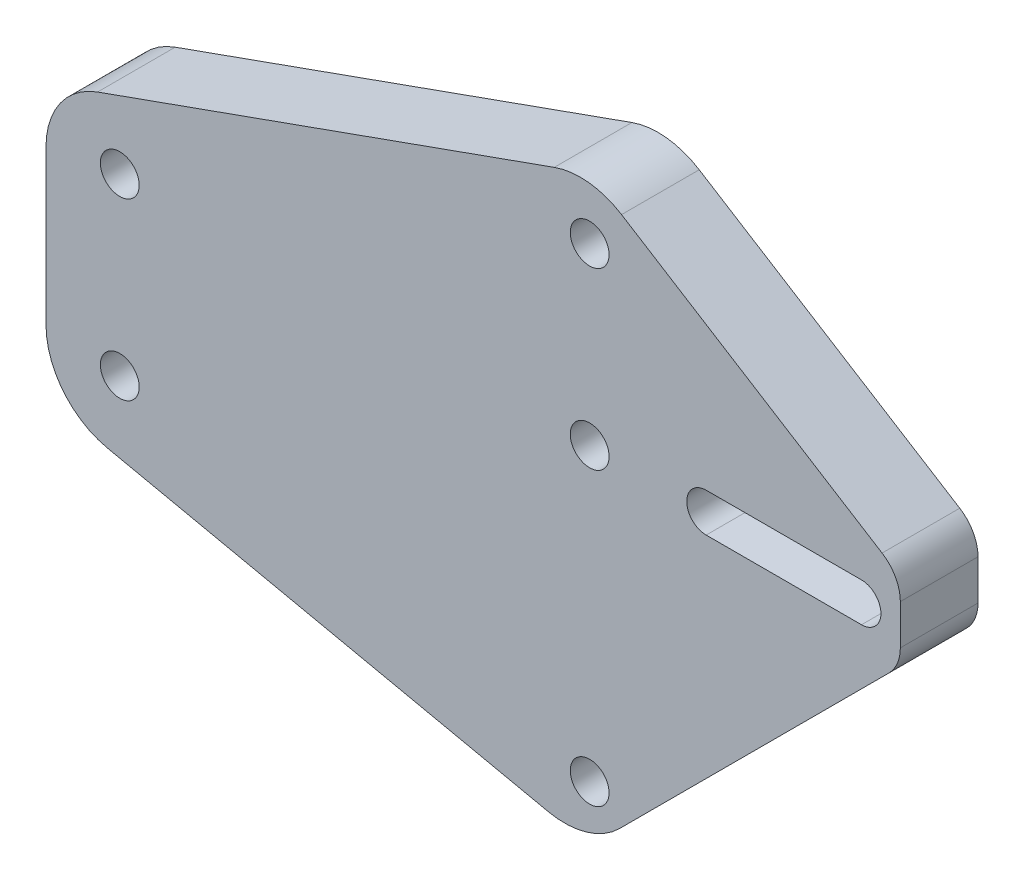
SolidWorks part; units mm, degrees
ref_plane "Front Plane" through (0, 0, 0) normal (0, 0, 1) x (1, 0, 0)
ref_plane "Top Plane" through (0, 0, 0) normal (0, 1, 0) x (1, 0, 0)
ref_plane "Right Plane" through (0, 0, 0) normal (1, 0, 0) x (0, 0, -1)
sketch "Sketch1" plane through (0, 0, 0) normal (0, 0, 1) x (1, 0, 0)
  line L1 (-44.5586, 33.3719) -> (-103.3634, 12.3702)
  line L2 (-110, 2.9528) -> (-110, -16.9158)
  line L3 (-102.0953, -26.6939) -> (-45.3195, -38.8601)
  line L4 (-36.1531, -36.1531) -> (-1.4645, -1.4645)
  line L5 (-35.8952, 32.4345) -> (-2.35, 11.4688)
  line L6 (0, 7.2288) -> (0, 2.0711)
  line L7 (-25, 4.6499) -> (-5, 4.6499) construction
  line L8 (-25, 7.1499) -> (-5, 7.1499)
  line L9 (-25, 2.1499) -> (-5, 2.1499)
  circle A0 centre (-40, 4.6499) radius 2.5
  arc A1 (-25, 7.1499) -> (-25, 2.1499) centre (-25, 4.6499) ccw
  arc A2 (-5, 2.1499) -> (-5, 7.1499) centre (-5, 4.6499) ccw
  circle A3 centre (-40, 27.1499) radius 2.5
  circle A4 centre (-100.5, 4.6499) radius 2.5
  circle A5 centre (-100.5, -17.8501) radius 2.5
  circle A6 centre (-40, -32.8501) radius 2.5
  arc A7 (-35.8952, 32.4345) -> (-44.5586, 33.3719) centre (-41.1952, 23.9545) ccw
  arc A8 (-45.3195, -38.8601) -> (-36.1531, -36.1531) centre (-43.2242, -29.0821) ccw
  arc A9 (-110, -16.9158) -> (-102.0953, -26.6939) centre (-100, -16.9158) ccw
  arc A10 (-103.3634, 12.3702) -> (-110, 2.9528) centre (-100, 2.9528) ccw
  arc A11 (0, 2.0711) -> (-1.4645, -1.4645) centre (-5, 2.0711) cw
  arc A12 (-2.35, 11.4688) -> (0, 7.2288) centre (-5, 7.2288) cw
  point P9 (0, 4.6499)
  point P11 (-15, 4.6499)
  point P44 (-40, 35)
  point P47 (-40, -40)
  point P50 (-110, -25)
  point P53 (-110, 10)
  point P56 (0, 0)
  point P59 (0, 10)
  dimension "D1" = 5
  dimension "D8" = 2.5
  dimension "D9" = 20
  dimension "D10" = 5
  dimension "D12" = 5
  dimension "D14" = 5
  dimension "D17" = 5
  dimension "D22" = 10
  dimension "D23" = 5
  dimension "D2" = 35
  dimension "D3" = 70
  dimension "D4" = 10
  dimension "D5" = 40
  dimension "D6" = 40
  dimension "D7" = 40
  dimension "D11" = 22.5
  dimension "D13" = 60.5
  dimension "D15" = 22.5
  dimension "D16" = 60
  dimension "D18" = 15
  dimension "D19" = 25
  dimension "D20" = 40
  dimension "D21" = 15
extrude "Boss-Extrude2" add sketch "Sketch1" along normal blind 10
